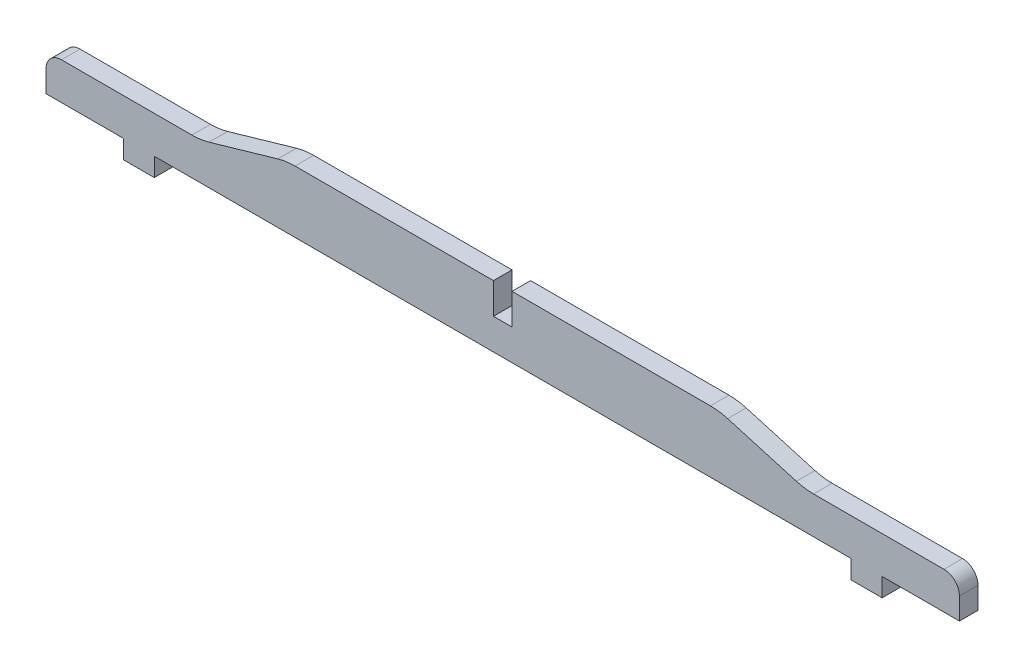
SolidWorks part; units mm, degrees
ref_plane "Front Plane" through (0, 0, 0) normal (0, 0, 1) x (1, 0, 0)
ref_plane "Top Plane" through (0, 0, 0) normal (0, 1, 0) x (1, 0, 0)
ref_plane "Right Plane" through (0, 0, 0) normal (1, 0, 0) x (0, 0, -1)
sketch "Sketch1" plane through (0, 0, 0) normal (0, 0, 1) x (1, 0, 0)
  line L0 (70, 0) -> (-70, 0)
  line L4 (112.6667, -20) -> (-112.6667, -20)
  line L5 (-147.6667, -20) -> (-122.6667, -20)
  line L6 (147.6667, -20) -> (122.6667, -20)
  line L7 (-122.6667, -20) -> (-122.6667, -26)
  line L8 (-122.6667, -26) -> (-112.6667, -26)
  line L9 (-112.6667, -26) -> (-112.6667, -20)
  line L10 (112.6667, -20) -> (112.6667, -26)
  line L11 (112.6667, -26) -> (122.6667, -26)
  line L12 (122.6667, -26) -> (122.6667, -20)
  line L13 (-147.6667, -20) -> (-147.6667, -8)
  line L14 (-147.6667, -8) -> (-97.6667, -8)
  line L15 (-97.6667, -8) -> (-70, 0)
  line L16 (70, 0) -> (97.6667, -8)
  line L17 (97.6667, -8) -> (147.6667, -8)
  line L18 (147.6667, -8) -> (147.6667, -20)
  point P4 (0, 0)
  point P10 (0, -20)
  dimension "D1" = 295.3333
  dimension "D2" = 20
  dimension "D3" = 6
  dimension "D4" = 10
  dimension "D7" = 12
  dimension "D5" = 50
  dimension "D6" = 140
  dimension "D8" = 25
extrude "Boss-Extrude1" add sketch "Sketch1" along normal blind 6
fillet "Fillet1" radius 5 2 edges at (147.6667, -8, 3) (-147.6667, -8, 3)
fillet "Fillet2" radius 20 4 edges at (97.6667, -8, 3) (70, 0, 3) (-70, 0, 3) (-97.6667, -8, 3)
sketch "Sketch2" plane through (0, 0, 6) normal (0, 0, 1) x (1, 0, 0)
  line L0 (0, 0) -> (0, -20) construction
  line L1 (67.1665, 0) -> (-67.1665, 0) construction
  line L2 (-112.6667, -20) -> (112.6667, -20) construction
  line L4 (-3, -10) -> (3, -10)
  line L5 (-3, -10) -> (-3, 0)
  line L6 (-3, 0) -> (3, 0)
  line L7 (3, -10) -> (3, 0)
  point P13 (0, -10)
  dimension "D1" = 6
extrude "Cut-Extrude1" cut sketch "Sketch2" against normal through all both and the other way through all
equation "\"D1@Sketch1\"=300-4.66666666"
